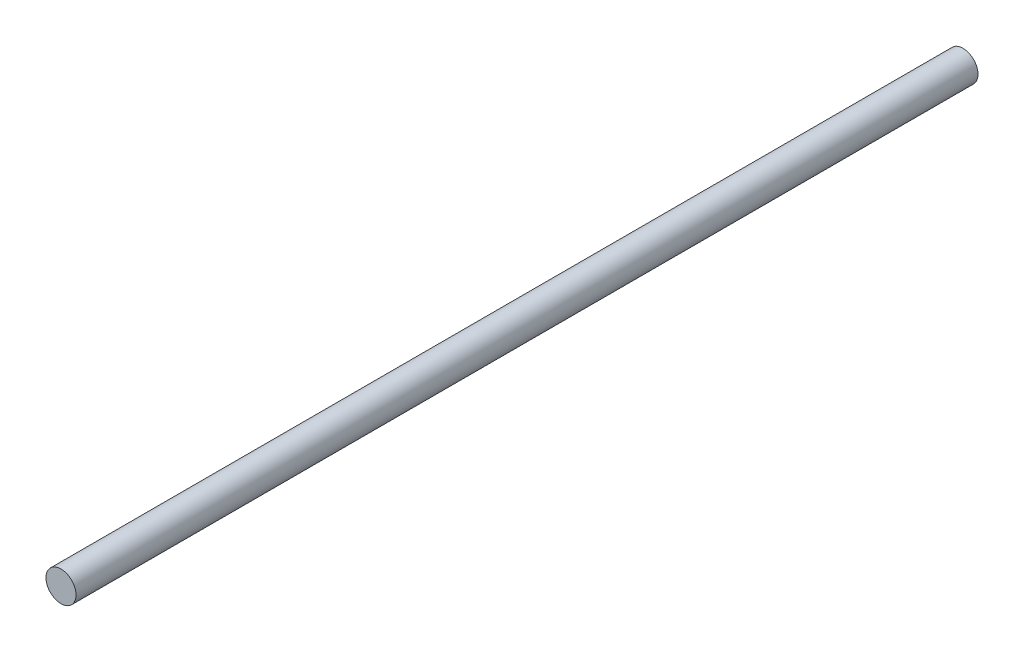
SolidWorks part; units mm, degrees
material "Nikiel"
ref_plane "Płaszczyzna przednia" through (0, 0, 0) normal (0, 0, 1) x (1, 0, 0)
ref_plane "Płaszczyzna górna" through (0, 0, 0) normal (0, 1, 0) x (1, 0, 0)
ref_plane "Płaszczyzna prawa" through (0, 0, 0) normal (1, 0, 0) x (0, 0, -1)
sketch "Szkic1" plane through (0, 0, 0) normal (0, 0, 1) x (1, 0, 0)
  circle A0 centre (0, 0) radius 1.5
extrude "Dodanie-wyciągnięcie1" add sketch "Szkic1" along normal blind 90
